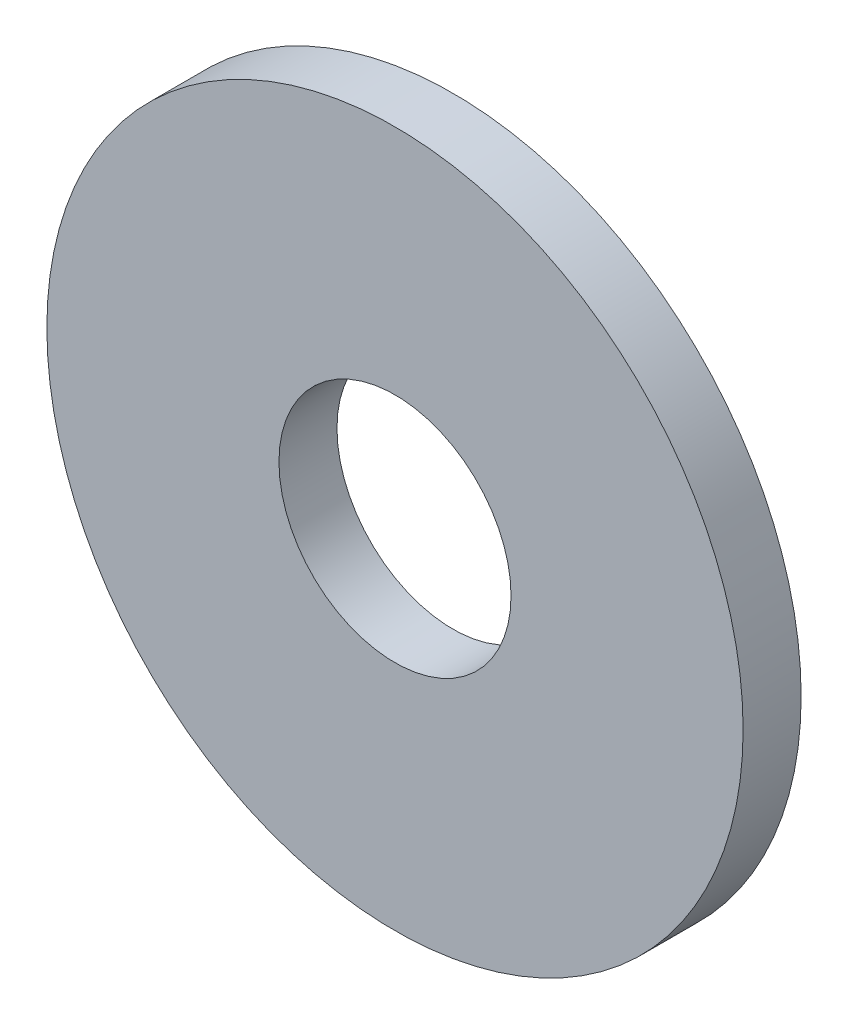
SolidWorks part; units mm, degrees
material "7075-O (SS)"
ref_plane "Płaszczyzna XY" through (0, 0, 0) normal (0, 0, 1) x (1, 0, 0)
ref_plane "Płaszczyzna XZ" through (0, 0, 0) normal (0, 1, 0) x (1, 0, 0)
ref_plane "Płaszczyzna YZ" through (0, 0, 0) normal (1, 0, 0) x (0, 0, -1)
sketch "Szkic1" plane through (0, 0, 0) normal (0, 0, 1) x (1, 0, 0)
  circle A0 centre (0, 0) radius 2
  circle A1 centre (0, 0) radius 6
  dimension "D1" = 4
  dimension "D2" = 12
extrude "Dodanie-wyciągnięcie1" add sketch "Szkic1" along normal blind 1
